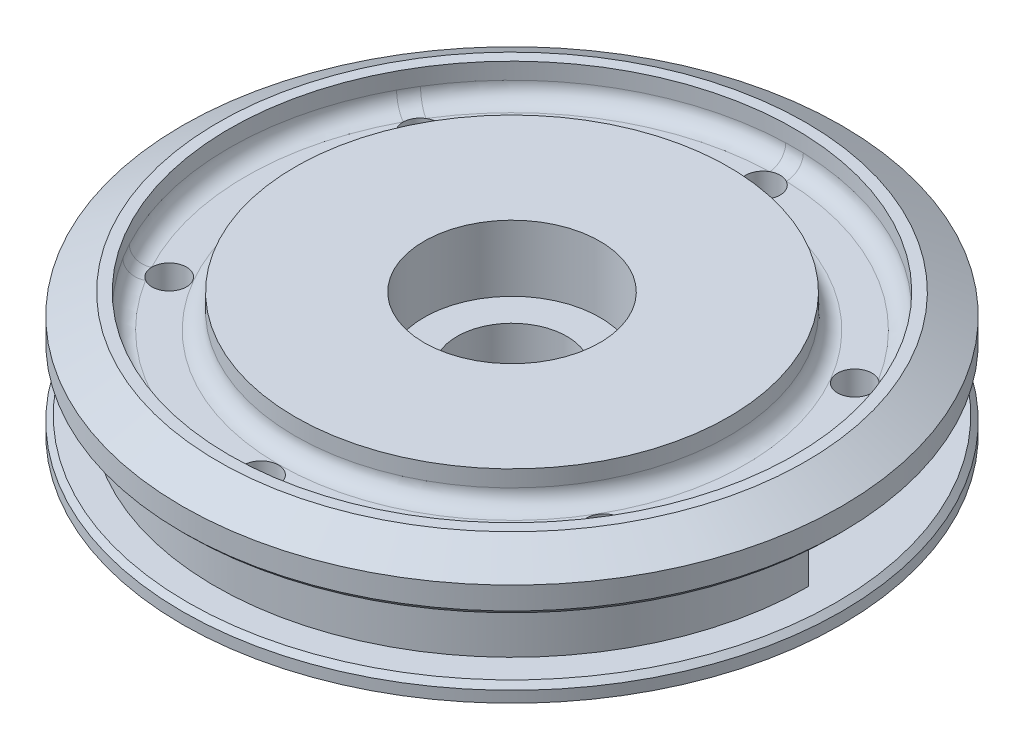
SolidWorks part; units mm, degrees
ref_plane "Front Plane" through (0, 0, 0) normal (0, 0, 1) x (1, 0, 0)
ref_plane "Top Plane" through (0, 0, 0) normal (0, 1, 0) x (1, 0, 0)
ref_plane "Right Plane" through (0, 0, 0) normal (1, 0, 0) x (0, 0, -1)
sketch "Sketch1" plane through (0, 0, 0) normal (0, 0, 1) x (1, 0, 0)
  line L0 (0, 0) -> (11.1125, 0)
  line L1 (11.1125, 0) -> (11.1125, 18.4277)
  line L2 (11.1125, 18.4277) -> (47.625, 18.4277)
  line L3 (47.625, 18.4277) -> (47.625, 20.809)
  line L4 (47.625, 20.809) -> (42.8625, 20.809)
  line L5 (42.8625, 20.809) -> (42.8625, 29.2077)
  line L6 (42.8625, 29.2077) -> (47.625, 29.2077)
  line L7 (47.625, 29.2077) -> (47.625, 36.2077)
  line L8 (47.625, 36.2077) -> (0, 36.2077)
  line L9 (0, 36.2077) -> (0, 0)
  dimension "D1" = 11.1125
  dimension "D2" = 47.625
  dimension "D3" = 42.8625
  dimension "D4" = 2.3813
  dimension "D5" = 18.4277
  dimension "D6" = 17.78
  dimension "D7" = 7
revolve "Revolve1" add sketch "Sketch1" angle 360 about L9
hole_wizard "#10-24 Tapped Hole1" positions "Sketch2" profile "Sketch3" tap size "#10-24" standard "ANSI Inch" end condition through all
sketch "Sketch2" plane through (0, 36.2077, 0) normal (0, 1, 0) x (1, 0, 0)
  point P0 (0, 0)
sketch "Sketch3" plane through (0, 36.2077, 0) normal (1, 0, 0) x (0, 0, 1)
  line L0 (0, 0) -> (0, 36.2077)
  line L1 (0, 36.2077) -> (1.8986, 36.2077)
  line L2 (1.8986, 36.2077) -> (1.8986, 0)
  line L5 (1.8986, 0) -> (0, 0)
  line L11 (0, -6.35) -> (0, 107.95) construction
  dimension "Thru Tap Drill Dia." = 3.7973
  dimension "Thru Tap Drill Depth" = 36.2077
cosmetic thread "Hole Thread1" parameters "D2"=4.826
chamfer "Chamfer1" distance 0.762 angle 45 2 edges at (0, 20.809, 47.625) (0, 29.2077, 47.625)
sketch "Sketch4" plane through (0, 36.2077, 0) normal (0, 1, 0) x (1, 0, 0)
  circle A0 centre (0, 0) radius 12.7
  dimension "D1" = 25.4
extrude "Cut-Extrude1" [suppressed] cut sketch "Sketch4" against normal offset from surface (38.8937 mm away) 4.7625
sketch "Sketch5" plane through (0, 36.2077, 0) normal (0, 1, 0) x (1, 0, 0)
  circle A0 centre (0, 0) radius 7.9375
  dimension "D1" = 15.875
extrude "Cut-Extrude2" cut sketch "Sketch5" against normal offset from surface (25.7077 mm away) 10.5 up to face at (0, 0, 1.8986)
ref_plane "Plane2" through (0, 0, -11.1125) normal (0, 0, -1) x (-1, 0, 0)
hole_wizard "#6-32 Tapped Hole2" positions "Sketch10" profile "Sketch11" tap size "#6-32" standard "ANSI Inch"
sketch "Sketch10" plane through (0, 0, -11.1125) normal (0, 0, -1) x (-1, 0, 0)
  line L0 (-47.625, 18.4277) -> (47.625, 18.4277) construction
  point P0 (0, 8.2677)
  dimension "D1" = 10.16
sketch "Sketch11" plane through (0, 8.2677, -11.1125) normal (1, 0, 0) x (0, 1, 0)
  line L0 (0, 0) -> (0, 9.2139)
  line L1 (0, 9.2139) -> (1.3525, 9.2139)
  line L2 (1.3525, 9.2139) -> (1.3525, 0)
  line L5 (1.3525, 0) -> (0, 0)
  line L11 (0, -6.35) -> (0, 107.95) construction
  dimension "Thru Tap Drill Dia." = 2.7051
  dimension "Thru Tap Drill Depth" = 9.2139
cosmetic thread "Hole Thread3" parameters "D1"=0, "D2"=3.7051
sketch "Sketch12" plane through (0, 36.2077, 0) normal (0, 1, 0) x (1, 0, 0)
  circle A0 centre (0, 0) radius 12.7
  dimension "D1" = 25.4
extrude "Cut-Extrude3" cut sketch "Sketch12" against normal blind 9.525
sketch "Sketch13" plane through (0, 29.2077, 0) normal (0, -1, 0) x (1, 0, 0)
  line L0 (36.5125, 0) -> (36.5125, -22.4506)
  line L1 (36.5125, 0) -> (42.8625, 0)
  circle A0 centre (0, 0) radius 42.8625 construction
  arc A1 (36.5125, -22.4506) -> (42.8625, 0) centre (0, 0) ccw
  dimension "D1" = 6.35
extrude "Cut-Extrude4" cut sketch "Sketch13" along normal up to surface (8.3987 mm away) up to face at (0, 20.809, -46.863)
sketch "Sketch14" plane through (0, 29.2077, 0) normal (0, -1, 0) x (1, 0, 0)
  line L0 (36.5125, 0) -> (36.5125, -22.4506) construction
  line L1 (36.5125, 0) -> (36.5125, -22.4506)
  line L2 (36.5125, 0) -> (35.1325, 0)
  line L3 (35.1325, 0) -> (35.1325, -8.5)
  line L4 (35.1325, -9.9804) -> (35.1325, -10.5)
  line L5 (35.1325, -11.9804) -> (35.1325, -12.5)
  line L6 (35.1325, -13.9804) -> (35.1325, -14.5)
  line L7 (35.1325, -15.9804) -> (35.1325, -16.5)
  line L8 (35.1325, -17.9804) -> (35.1325, -18.5)
  line L9 (35.1325, -19.9804) -> (35.1325, -20.5)
  line L15 (35.1325, -21.9804) -> (35.1325, -22.5)
  line L16 (35.1325, -22.5) -> (35.1325, -24.554)
  line L17 (35.1325, -7) -> (36.5125, -7)
  arc A0 (35.5707, -9.7391) -> (35.5707, -8.7413) centre (35.3275, -9.2402) ccw
  arc A1 (35.5707, -9.7391) -> (35.2629, -9.8316) centre (35.1325, -8.8402) cw
  arc A2 (35.5707, -8.7413) -> (35.2629, -8.6487) centre (35.1325, -9.6402) ccw
  arc A3 (35.2629, -8.6487) -> (35.1325, -8.5) centre (35.2825, -8.5) cw
  arc A4 (35.2629, -9.8316) -> (35.1325, -9.9804) centre (35.2825, -9.9804) ccw
  arc A5 (35.2629, -10.6487) -> (35.1325, -10.5) centre (35.2825, -10.5) cw
  arc A6 (35.5707, -10.7413) -> (35.2629, -10.6487) centre (35.1325, -11.6402) ccw
  arc A7 (35.5707, -11.7391) -> (35.5707, -10.7413) centre (35.3275, -11.2402) ccw
  arc A8 (35.5707, -11.7391) -> (35.2629, -11.8316) centre (35.1325, -10.8402) cw
  arc A9 (35.2629, -11.8316) -> (35.1325, -11.9804) centre (35.2825, -11.9804) ccw
  arc A10 (35.2629, -12.6487) -> (35.1325, -12.5) centre (35.2825, -12.5) cw
  arc A11 (35.5707, -12.7413) -> (35.2629, -12.6487) centre (35.1325, -13.6402) ccw
  arc A12 (35.5707, -13.7391) -> (35.5707, -12.7413) centre (35.3275, -13.2402) ccw
  arc A13 (35.5707, -13.7391) -> (35.2629, -13.8316) centre (35.1325, -12.8402) cw
  arc A14 (35.2629, -13.8316) -> (35.1325, -13.9804) centre (35.2825, -13.9804) ccw
  arc A15 (35.2629, -14.6487) -> (35.1325, -14.5) centre (35.2825, -14.5) cw
  arc A16 (35.5707, -14.7413) -> (35.2629, -14.6487) centre (35.1325, -15.6402) ccw
  arc A17 (35.5707, -15.7391) -> (35.5707, -14.7413) centre (35.3275, -15.2402) ccw
  arc A18 (35.5707, -15.7391) -> (35.2629, -15.8316) centre (35.1325, -14.8402) cw
  arc A19 (35.2629, -15.8316) -> (35.1325, -15.9804) centre (35.2825, -15.9804) ccw
  arc A20 (35.2629, -16.6487) -> (35.1325, -16.5) centre (35.2825, -16.5) cw
  arc A21 (35.5707, -16.7413) -> (35.2629, -16.6487) centre (35.1325, -17.6402) ccw
  arc A22 (35.5707, -17.7391) -> (35.5707, -16.7413) centre (35.3275, -17.2402) ccw
  arc A23 (35.5707, -17.7391) -> (35.2629, -17.8316) centre (35.1325, -16.8402) cw
  arc A24 (35.2629, -17.8316) -> (35.1325, -17.9804) centre (35.2825, -17.9804) ccw
  arc A25 (35.2629, -18.6487) -> (35.1325, -18.5) centre (35.2825, -18.5) cw
  arc A26 (35.5707, -18.7413) -> (35.2629, -18.6487) centre (35.1325, -19.6402) ccw
  arc A27 (35.5707, -19.7391) -> (35.5707, -18.7413) centre (35.3275, -19.2402) ccw
  arc A28 (35.5707, -19.7391) -> (35.2629, -19.8316) centre (35.1325, -18.8402) cw
  arc A29 (35.2629, -19.8316) -> (35.1325, -19.9804) centre (35.2825, -19.9804) ccw
  arc A52 (42.8625, 0) -> (36.5125, -22.4506) centre (0, 0) ccw construction
  arc A53 (36.5125, -22.4506) -> (35.1325, -24.554) centre (0, 0) cw
  arc A54 (35.2629, -20.6487) -> (35.1325, -20.5) centre (35.2825, -20.5) cw
  arc A55 (35.5707, -20.7413) -> (35.2629, -20.6487) centre (35.1325, -21.6402) ccw
  arc A56 (35.5707, -21.7391) -> (35.5707, -20.7413) centre (35.3275, -21.2402) ccw
  arc A57 (35.5707, -21.7391) -> (35.2629, -21.8316) centre (35.1325, -20.8402) cw
  arc A58 (35.2629, -21.8316) -> (35.1325, -21.9804) centre (35.2825, -21.9804) ccw
  point P15 (35.8825, -9.2402)
  arc M4 (36.5125, -22.4506) -> (42.8625, 0) centre (0, 0) cw
  dimension "D2" = 0.555
  dimension "D3" = 1
  dimension "D1" = 1.38
  dimension "D4" = 0.4
  dimension "D6" = 0.75
  dimension "D5" = 2
  dimension "D8" = 0.15
  dimension "D10" = 1.5
  dimension "D7" = 7
  dimension "D9" = 7
extrude "Cut-Extrude5" [suppressed] cut sketch "Sketch14" along normal up to surface (13.0175 mm away) contours A57 A58 L15 L16 L1 L17 L3 A3 A2 A0 A1 A4 L4 A5 A6 A7 A8 A9 L5 A10 A11 A12 A13 A14 L6 A15 A16 A17 A18 A19 L7 A20 A21 A22 A23 A24 L8 A25 A26 A27 A28 A29 L9 A54 A55 A56 M4
hole_wizard "#6-32 Tapped Hole1" positions "Sketch15" profile "Sketch17" tap size "#6-32" standard "ANSI Inch"
sketch "Sketch15" plane through (36.5125, 0, 0) normal (1, 0, 0) x (0, 0, -1)
  line L0 (7, 20.809) -> (0, 29.2077)
  line L1 (0, 20.809) -> (22.4506, 20.809) construction
  line L2 (0, 20.809) -> (0, 29.2077) construction
  point P0 (3.5, 25.0083)
  point P7 (0, 0)
  point P8 (6.2042, 20.809)
  dimension "D1" = 7
sketch "Sketch17" plane through (36.5125, 25.0083, -3.5) normal (0, 1, 0) x (0, 0, -1)
  line L0 (0, 0) -> (0, 15.8127)
  line L1 (0, 15.8127) -> (1.3525, 15)
  line L2 (1.3525, 15) -> (1.3525, 0)
  line L5 (1.3525, 0) -> (0, 0)
  line L10 (0, 15.8127) -> (-1.3526, 15) construction
  line L11 (0, -6.35) -> (0, 107.95) construction
  dimension "Tap Drill Dia." = 2.7051
  dimension "Tap Drill Depth" = 15
  dimension "Drill Angle" = 118
cosmetic thread "Hole Thread2" parameters "D1"=7.01, "D2"=3.5052
surface "Surface-Offset1" [suppressed] parameters "D1"=0.3
split "Split1" [suppressed] bodies to split 114
delete or keep bodies "Body-Delete/Keep 1" [suppressed] type delete bodies bodies 116
sketch "Sketch18" plane through (0, 0, 0) normal (0, -1, 0) x (1, 0, 0)
  circle A0 centre (0, 0) radius 3.475
  dimension "D1" = 6.95
extrude "Cut-Extrude6" cut sketch "Sketch18" against normal blind 1.778
hole_wizard "#10 Clearance Hole1" positions "Sketch20" profile "Sketch22" hole size "#10" standard "ANSI Inch" end condition up to next
sketch "Sketch20" plane through (0, 18.4277, 0) normal (0, -1, 0) x (-1, 0, 0)
  point P0 (0, -36.2458)
  point P4 (0, 0)
  dimension "D1" = 36.2458
sketch "Sketch22" plane through (0, 18.4277, 36.2458) normal (1, 0, 0) x (0, 0, -1)
  line L0 (0, 0) -> (0, 17.781)
  line L1 (0, 17.781) -> (2.4892, 17.781)
  line L2 (2.4892, 17.781) -> (2.4892, 0)
  line L5 (2.4892, 0) -> (0, 0)
  line L11 (0, -6.35) -> (0, 107.95) construction
  dimension "Thru Hole Dia." = 4.9784
  dimension "Thru Hole Depth" = 17.781
pattern_circular "CirPattern1" count 6 over 360 about axis through (0, 0, 0) along (0, 1, 0) of "#10 Clearance Hole1"
chamfer "Chamfer2" distance 3 angle 60 1 edges at (0, 36.2077, 47.625)
sketch "Sketch23" plane through (0, 36.2077, 0) normal (0, 1, 0) x (1, 0, 0)
  circle A0 centre (0, 0) radius 31.3055
  circle A1 centre (0, 0) radius 40.8305
  dimension "D1" = 81.661
  dimension "D2" = 9.525
extrude "Cut-Extrude7" cut sketch "Sketch23" against normal blind 4.7625
fillet "Fillet1" radius 2.3813 2 edges at (0, 31.4452, 31.3055) (0, 31.4452, 40.8305)
fillet "Fillet2" radius 4.7625 1 edges at (36.5125, 25.0083, -22.4506)
equation "\"D1@Sketch12\"=1in"
equation "\"D1@Sketch14\"=1.38mm"
equation "\"D1@Sketch23\"=1.42in*2+.375in"
